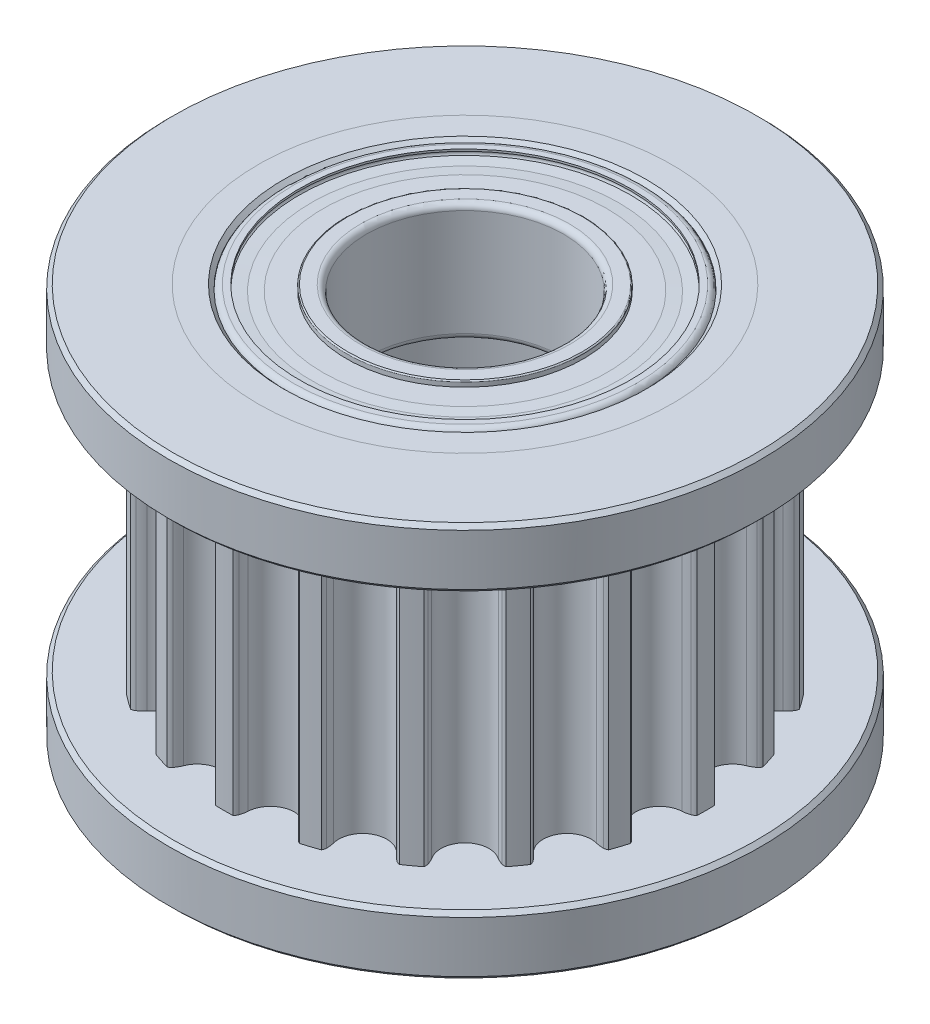
SolidWorks part; units mm, degrees
material "6061-T6 (SS)"
ref_plane "Přední rovina" through (0, 0, 0) normal (0, 0, 1) x (1, 0, 0)
ref_plane "Horní rovina" through (0, 0, 0) normal (0, 1, 0) x (1, 0, 0)
ref_plane "Pravá rovina" through (0, 0, 0) normal (1, 0, 0) x (0, 0, -1)
sketch "Skica1" plane through (0, 0, 0) normal (0, 0, 1) x (1, 0, 0)
  line L0 (4.5, 10) -> (5.25, 10)
  line L1 (5.25, 10) -> (5.25, 8.5)
  line L2 (5.25, 8.5) -> (6.11, 8.5)
  line L3 (6.11, 8.5) -> (6.11, 1.5)
  line L4 (6.11, 1.5) -> (5.25, 1.5)
  line L5 (5.25, 1.5) -> (5.25, 0)
  line L6 (5.25, 0) -> (4.5, 0)
  line L8 (4.5, 10) -> (4.5, 7)
  line L9 (4.5, 7) -> (3.5, 7)
  line L10 (3.5, 7) -> (3.5, 3)
  line L11 (3.5, 3) -> (4.5, 3)
  line L12 (4.5, 3) -> (4.5, 0)
  line L13 (0, 0) -> (0, -4.1646) construction
  dimension "D1" = 10
  dimension "D2" = 7
  dimension "D3" = 4.5
  dimension "D4" = 3.5
  dimension "D5" = 6.11
  dimension "D6" = 3
  dimension "D7" = 5.25
revolve "Rotovat1" add sketch "Skica1" angle 360 about L13
chamfer "Zkosení1" distance 0.1 angle 45 4 edges at (0, 3, 3.5) (0, 0, 4.5) (0, 7, 3.5) (0, 10, 4.5)
fillet "Zaoblit1" radius 0.1 2 edges at (0, 3, 4.5) (0, 7, 4.5)
sketch "Skica11" plane through (0, 8.5, 0) normal (0, 1, 0) x (1, 0, 0)
  line L0 (0, -5.5) -> (0, 5.5) construction
  line L1 (-5.5, 0) -> (5.5, 0) construction
  point P5 (0, 6.1087)
  arc B0 (-3.6824, -4.5256) -> (-4.5256, -3.6824) centre (-4.1938, -4.1938) ccw
  arc B1 (-3.6824, -4.5256) -> (-3.7624, -4.7003) centre (-3.1284, -4.885) ccw
  arc B2 (-3.7624, -4.7003) -> (-3.7672, -4.8088) centre (-3.5429, -4.7643) ccw
  arc B3 (-3.7672, -4.8088) -> (-3.4093, -5.0688) centre (0, 0) ccw
  arc B4 (-3.4093, -5.0688) -> (-3.3076, -5.0308) centre (-3.4362, -4.8418) ccw
  arc B5 (-3.3076, -5.0308) -> (-3.1662, -4.9006) centre (-3.6792, -4.4848) ccw
  arc B6 (-2.1037, -5.442) -> (-3.1662, -4.9006) centre (-2.6926, -5.2845) ccw
  arc B7 (-2.1037, -5.442) -> (-2.1258, -5.6329) centre (-1.4657, -5.6126) ccw
  arc B8 (-2.1258, -5.6329) -> (-2.0968, -5.7376) centre (-1.8973, -5.6259) ccw
  arc B9 (-2.0968, -5.7376) -> (-1.6761, -5.8742) centre (0, 0) ccw
  arc B10 (-1.6761, -5.8742) -> (-1.5911, -5.8066) centre (-1.7719, -5.6667) ccw
  arc B11 (-1.5911, -5.8066) -> (-1.4968, -5.6392) centre (-2.1132, -5.4022) ccw
  arc B12 (-0.319, -5.8257) -> (-1.4968, -5.6392) centre (-0.9278, -5.8579) ccw
  arc B13 (-0.319, -5.8257) -> (-0.2811, -6.0141) centre (0.3404, -5.7909) ccw
  arc B14 (-0.2811, -6.0141) -> (-0.2211, -6.1047) centre (-0.0659, -5.9369) ccw
  arc B15 (-0.2211, -6.1047) -> (0.2211, -6.1047) centre (0, 0) ccw
  arc B16 (0.2211, -6.1047) -> (0.2811, -6.0141) centre (0.0659, -5.9369) ccw
  arc B17 (0.2811, -6.0141) -> (0.319, -5.8257) centre (-0.3404, -5.7909) ccw
  arc B18 (1.4968, -5.6392) -> (0.319, -5.8257) centre (0.9278, -5.8579) ccw
  arc B19 (1.4968, -5.6392) -> (1.5911, -5.8066) centre (2.1132, -5.4022) ccw
  arc B20 (1.5911, -5.8066) -> (1.6761, -5.8742) centre (1.7719, -5.6667) ccw
  arc B21 (1.6761, -5.8742) -> (2.0968, -5.7376) centre (0, 0) ccw
  arc B22 (2.0968, -5.7376) -> (2.1258, -5.6329) centre (1.8973, -5.6259) ccw
  arc B23 (2.1258, -5.6329) -> (2.1037, -5.442) centre (1.4657, -5.6126) ccw
  arc B24 (3.1662, -4.9006) -> (2.1037, -5.442) centre (2.6926, -5.2845) ccw
  arc B25 (3.1662, -4.9006) -> (3.3076, -5.0308) centre (3.6792, -4.4848) ccw
  arc B26 (3.3076, -5.0308) -> (3.4093, -5.0688) centre (3.4362, -4.8418) ccw
  arc B27 (3.4093, -5.0688) -> (3.7672, -4.8088) centre (0, 0) ccw
  arc B28 (3.7672, -4.8088) -> (3.7624, -4.7003) centre (3.5429, -4.7643) ccw
  arc B29 (3.7624, -4.7003) -> (3.6824, -4.5256) centre (3.1284, -4.885) ccw
  arc B30 (4.5256, -3.6824) -> (3.6824, -4.5256) centre (4.1938, -4.1938) ccw
  arc B31 (4.5256, -3.6824) -> (4.7003, -3.7624) centre (4.885, -3.1284) ccw
  arc B32 (4.7003, -3.7624) -> (4.8088, -3.7672) centre (4.7643, -3.5429) ccw
  arc B33 (4.8088, -3.7672) -> (5.0688, -3.4093) centre (0, 0) ccw
  arc B34 (5.0688, -3.4093) -> (5.0308, -3.3076) centre (4.8418, -3.4362) ccw
  arc B35 (5.0308, -3.3076) -> (4.9006, -3.1662) centre (4.4848, -3.6792) ccw
  arc B36 (5.442, -2.1037) -> (4.9006, -3.1662) centre (5.2845, -2.6926) ccw
  arc B37 (5.442, -2.1037) -> (5.6329, -2.1258) centre (5.6126, -1.4657) ccw
  arc B38 (5.6329, -2.1258) -> (5.7376, -2.0968) centre (5.6259, -1.8973) ccw
  arc B39 (5.7376, -2.0968) -> (5.8742, -1.6761) centre (0, 0) ccw
  arc B40 (5.8742, -1.6761) -> (5.8066, -1.5911) centre (5.6667, -1.7719) ccw
  arc B41 (5.8066, -1.5911) -> (5.6392, -1.4968) centre (5.4022, -2.1132) ccw
  arc B42 (5.8257, -0.319) -> (5.6392, -1.4968) centre (5.8579, -0.9278) ccw
  arc B43 (5.8257, -0.319) -> (6.0141, -0.2811) centre (5.7909, 0.3404) ccw
  arc B44 (6.0141, -0.2811) -> (6.1047, -0.2211) centre (5.9369, -0.0659) ccw
  arc B45 (6.1047, -0.2211) -> (6.1047, 0.2211) centre (0, 0) ccw
  arc B46 (6.1047, 0.2211) -> (6.0141, 0.2811) centre (5.9369, 0.0659) ccw
  arc B47 (6.0141, 0.2811) -> (5.8257, 0.319) centre (5.7909, -0.3404) ccw
  arc B48 (5.6392, 1.4968) -> (5.8257, 0.319) centre (5.8579, 0.9278) ccw
  arc B49 (5.6392, 1.4968) -> (5.8066, 1.5911) centre (5.4022, 2.1132) ccw
  arc B50 (5.8066, 1.5911) -> (5.8742, 1.6761) centre (5.6667, 1.7719) ccw
  arc B51 (5.8742, 1.6761) -> (5.7376, 2.0968) centre (0, 0) ccw
  arc B52 (5.7376, 2.0968) -> (5.6329, 2.1258) centre (5.6259, 1.8973) ccw
  arc B53 (5.6329, 2.1258) -> (5.442, 2.1037) centre (5.6126, 1.4657) ccw
  arc B54 (4.9006, 3.1662) -> (5.442, 2.1037) centre (5.2845, 2.6926) ccw
  arc B55 (4.9006, 3.1662) -> (5.0308, 3.3076) centre (4.4848, 3.6792) ccw
  arc B56 (5.0308, 3.3076) -> (5.0688, 3.4093) centre (4.8418, 3.4362) ccw
  arc B57 (5.0688, 3.4093) -> (4.8088, 3.7672) centre (0, 0) ccw
  arc B58 (4.8088, 3.7672) -> (4.7003, 3.7624) centre (4.7643, 3.5429) ccw
  arc B59 (4.7003, 3.7624) -> (4.5256, 3.6824) centre (4.885, 3.1284) ccw
  arc B60 (3.6824, 4.5256) -> (4.5256, 3.6824) centre (4.1938, 4.1938) ccw
  arc B61 (3.6824, 4.5256) -> (3.7624, 4.7003) centre (3.1284, 4.885) ccw
  arc B62 (3.7624, 4.7003) -> (3.7672, 4.8088) centre (3.5429, 4.7643) ccw
  arc B63 (3.7672, 4.8088) -> (3.4093, 5.0688) centre (0, 0) ccw
  arc B64 (3.4093, 5.0688) -> (3.3076, 5.0308) centre (3.4362, 4.8418) ccw
  arc B65 (3.3076, 5.0308) -> (3.1662, 4.9006) centre (3.6792, 4.4848) ccw
  arc B66 (2.1037, 5.442) -> (3.1662, 4.9006) centre (2.6926, 5.2845) ccw
  arc B67 (2.1037, 5.442) -> (2.1258, 5.6329) centre (1.4657, 5.6126) ccw
  arc B68 (2.1258, 5.6329) -> (2.0968, 5.7376) centre (1.8973, 5.6259) ccw
  arc B69 (2.0968, 5.7376) -> (1.6761, 5.8742) centre (0, 0) ccw
  arc B70 (1.6761, 5.8742) -> (1.5911, 5.8066) centre (1.7719, 5.6667) ccw
  arc B71 (1.5911, 5.8066) -> (1.4968, 5.6392) centre (2.1132, 5.4022) ccw
  arc B72 (0.319, 5.8257) -> (1.4968, 5.6392) centre (0.9278, 5.8579) ccw
  arc B73 (0.319, 5.8257) -> (0.2811, 6.0141) centre (-0.3404, 5.7909) ccw
  arc B74 (0.2811, 6.0141) -> (0.2211, 6.1047) centre (0.0659, 5.9369) ccw
  arc B75 (0.2211, 6.1047) -> (-0.2211, 6.1047) centre (0, 0) ccw
  arc B76 (-0.2211, 6.1047) -> (-0.2811, 6.0141) centre (-0.0659, 5.9369) ccw
  arc B77 (-0.2811, 6.0141) -> (-0.319, 5.8257) centre (0.3404, 5.7909) ccw
  arc B78 (-1.4968, 5.6392) -> (-0.319, 5.8257) centre (-0.9278, 5.8579) ccw
  arc B79 (-1.4968, 5.6392) -> (-1.5911, 5.8066) centre (-2.1132, 5.4022) ccw
  arc B80 (-1.5911, 5.8066) -> (-1.6761, 5.8742) centre (-1.7719, 5.6667) ccw
  arc B81 (-1.6761, 5.8742) -> (-2.0968, 5.7376) centre (0, 0) ccw
  arc B82 (-2.0968, 5.7376) -> (-2.1258, 5.6329) centre (-1.8973, 5.6259) ccw
  arc B83 (-2.1258, 5.6329) -> (-2.1037, 5.442) centre (-1.4657, 5.6126) ccw
  arc B84 (-3.1662, 4.9006) -> (-2.1037, 5.442) centre (-2.6926, 5.2845) ccw
  arc B85 (-3.1662, 4.9006) -> (-3.3076, 5.0308) centre (-3.6792, 4.4848) ccw
  arc B86 (-3.3076, 5.0308) -> (-3.4093, 5.0688) centre (-3.4362, 4.8418) ccw
  arc B87 (-3.4093, 5.0688) -> (-3.7672, 4.8088) centre (0, 0) ccw
  arc B88 (-3.7672, 4.8088) -> (-3.7624, 4.7003) centre (-3.5429, 4.7643) ccw
  arc B89 (-3.7624, 4.7003) -> (-3.6824, 4.5256) centre (-3.1284, 4.885) ccw
  arc B90 (-4.5256, 3.6824) -> (-3.6824, 4.5256) centre (-4.1938, 4.1938) ccw
  arc B91 (-4.5256, 3.6824) -> (-4.7003, 3.7624) centre (-4.885, 3.1284) ccw
  arc B92 (-4.7003, 3.7624) -> (-4.8088, 3.7672) centre (-4.7643, 3.5429) ccw
  arc B93 (-4.8088, 3.7672) -> (-5.0688, 3.4093) centre (0, 0) ccw
  arc B94 (-5.0688, 3.4093) -> (-5.0308, 3.3076) centre (-4.8418, 3.4362) ccw
  arc B95 (-5.0308, 3.3076) -> (-4.9006, 3.1662) centre (-4.4848, 3.6792) ccw
  arc B96 (-5.442, 2.1037) -> (-4.9006, 3.1662) centre (-5.2845, 2.6926) ccw
  arc B97 (-5.442, 2.1037) -> (-5.6329, 2.1258) centre (-5.6126, 1.4657) ccw
  arc B98 (-5.6329, 2.1258) -> (-5.7376, 2.0968) centre (-5.6259, 1.8973) ccw
  arc B99 (-5.7376, 2.0968) -> (-5.8742, 1.6761) centre (0, 0) ccw
  arc B100 (-5.8742, 1.6761) -> (-5.8066, 1.5911) centre (-5.6667, 1.7719) ccw
  arc B101 (-5.8066, 1.5911) -> (-5.6392, 1.4968) centre (-5.4022, 2.1132) ccw
  arc B102 (-5.8257, 0.319) -> (-5.6392, 1.4968) centre (-5.8579, 0.9278) ccw
  arc B103 (-5.8257, 0.319) -> (-6.0141, 0.2811) centre (-5.7909, -0.3404) ccw
  arc B104 (-6.0141, 0.2811) -> (-6.1047, 0.2211) centre (-5.9369, 0.0659) ccw
  arc B105 (-6.1047, 0.2211) -> (-6.1047, -0.2211) centre (0, 0) ccw
  arc B106 (-6.1047, -0.2211) -> (-6.0141, -0.2811) centre (-5.9369, -0.0659) ccw
  arc B107 (-6.0141, -0.2811) -> (-5.8257, -0.319) centre (-5.7909, 0.3404) ccw
  arc B108 (-5.6392, -1.4968) -> (-5.8257, -0.319) centre (-5.8579, -0.9278) ccw
  arc B109 (-5.6392, -1.4968) -> (-5.8066, -1.5911) centre (-5.4022, -2.1132) ccw
  arc B110 (-5.8066, -1.5911) -> (-5.8742, -1.6761) centre (-5.6667, -1.7719) ccw
  arc B111 (-5.8742, -1.6761) -> (-5.7376, -2.0968) centre (0, 0) ccw
  arc B112 (-5.7376, -2.0968) -> (-5.6329, -2.1258) centre (-5.6259, -1.8973) ccw
  arc B113 (-5.6329, -2.1258) -> (-5.442, -2.1037) centre (-5.6126, -1.4657) ccw
  arc B114 (-4.9006, -3.1662) -> (-5.442, -2.1037) centre (-5.2845, -2.6926) ccw
  arc B115 (-4.9006, -3.1662) -> (-5.0308, -3.3076) centre (-4.4848, -3.6792) ccw
  arc B116 (-5.0308, -3.3076) -> (-5.0688, -3.4093) centre (-4.8418, -3.4362) ccw
  arc B117 (-5.0688, -3.4093) -> (-4.8088, -3.7672) centre (0, 0) ccw
  arc B118 (-4.8088, -3.7672) -> (-4.7003, -3.7624) centre (-4.7643, -3.5429) ccw
  arc B119 (-4.7003, -3.7624) -> (-4.5256, -3.6824) centre (-4.885, -3.1284) ccw
sketch_block_instance "Blok1-1"
sketch_block "Blok1"
extrude "Odebrat vysunutím1" cut sketch "Skica11" against normal through all flip side to cut
sketch "Skica10" plane through (0, 10, 0) normal (0, 1, 0) x (1, 0, 0)
  circle A0 centre (0, 0) radius 7.5
  circle A1 centre (0, 0) radius 5.25 construction
  circle A2 centre (0, 0) radius 5.25
  dimension "D1" = 15
extrude "Přidat vysunutím1" add sketch "Skica10" against normal up to surface (1.5 mm away) separate body up to face at (0, 8.5, 5.25)
sketch "Skica12" plane through (0, 0, 0) normal (0, -1, 0) x (1, 0, 0)
  circle A0 centre (0, 0) radius 7.5
  circle A1 centre (0, 0) radius 5.25 construction
  circle A2 centre (0, 0) radius 5.25
  circle A3 centre (0, 0) radius 7.5 construction
extrude "Přidat vysunutím2" add sketch "Skica12" against normal up to surface (1.5 mm away) separate body up to face at (0, 1.5, 5.25)
chamfer "Zkosení2" distance 0.1 angle 45 2 edges at (0, 8.5, -7.5) (0, 10, 7.5)
chamfer "Zkosení3" distance 0.1 angle 45 2 edges at (0, 0, -7.5) (0, 1.5, 7.5)
sketch "Skica4" plane through (0, 0, 0) normal (0, 0, 1) x (1, 0, 0)
  line L0 (4.5, 9.85) -> (4.5, 7.15)
  line L1 (4.35, 7) -> (4.2, 7)
  line L2 (4.2, 7) -> (4.2, 7.05)
  line L3 (3.85, 7.2828) -> (4.2132, 7.229)
  line L4 (3.85, 7.2828) -> (3.85, 8.0528)
  line L5 (3.85, 8.9472) -> (3.85, 9.7172)
  line L6 (3.85, 9.7172) -> (4.2132, 9.771)
  line L7 (4.35, 10) -> (4.2, 10)
  line L8 (4.2, 10) -> (4.2, 9.95)
  line L9 (0, 0) -> (0, 18.4294) construction
  line L10 (4.4, 7) -> (-4.4, 7) construction
  arc A0 (4.35, 10) -> (4.5, 9.85) centre (4.35, 9.85) cw
  arc A1 (4.35, 7) -> (4.5, 7.15) centre (4.35, 7.15) ccw
  arc A2 (4.2, 9.95) -> (4.2132, 9.771) centre (4.2, 9.86) cw
  arc A3 (3.85, 8.9472) -> (3.85, 8.0528) centre (3.45, 8.5) cw
  arc A4 (4.2, 7.05) -> (4.2132, 7.229) centre (4.2, 7.14) ccw
  point P26 (4.5, 8.5)
  point P29 (4.275, 7)
  dimension "D3" = 0.09
  dimension "D6" = 0.15
  dimension "D7" = 0.6
  dimension "D1" = 4.5
  dimension "D2" = 3.85
  dimension "D4" = 0.05
  dimension "D5" = 0.15
  dimension "D8" = 0.77
  dimension "D9" = 3
  dimension "D10" = 1.05
revolve "Rotovat2" add sketch "Skica4" angle 360 about L9
sketch "Skica5" plane through (0, 0, 0) normal (0, 0, 1) x (1, 0, 0)
  line L0 (2.5, 9.85) -> (2.5, 7.15)
  line L1 (2.65, 10) -> (2.97, 10)
  line L2 (3, 9.97) -> (3, 9.86)
  line L3 (3, 9.86) -> (3.6, 9.86)
  line L4 (3.6, 9.86) -> (3.9, 9.84)
  line L5 (3.9, 9.84) -> (4.2, 9.86)
  line L6 (4.2, 9.86) -> (4.2, 9.81)
  line L7 (4.2, 9.81) -> (3.9, 9.77)
  line L8 (3.9, 9.77) -> (3.6, 9.77)
  line L9 (3.6, 9.77) -> (3, 9.81)
  line L10 (3, 9.81) -> (3, 8.8969)
  line L11 (2.65, 7) -> (2.97, 7)
  line L12 (0, 0) -> (0, 20.363) construction
  line L13 (3, 7.03) -> (3, 7.14)
  line L21 (3, 7.19) -> (3, 8.1031)
  line L22 (3, 7.14) -> (3.6, 7.14)
  line L23 (3.6, 7.14) -> (3.8962, 7.1917)
  line L24 (3.8962, 7.1917) -> (4.1924, 7.14)
  line L25 (4.1924, 7.14) -> (4.1924, 7.19)
  line L26 (4.1924, 7.19) -> (3.8975, 7.2581)
  line L27 (3.8975, 7.2581) -> (3.5975, 7.2581)
  line L28 (3.5975, 7.2581) -> (3, 7.19)
  line L29 (-4.2, 7) -> (4.2, 7) construction
  arc A0 (2.65, 7) -> (2.5, 7.15) centre (2.65, 7.15) cw
  arc A1 (2.65, 10) -> (2.5, 9.85) centre (2.65, 9.85) ccw
  arc A2 (3, 9.97) -> (2.97, 10) centre (2.97, 9.97) ccw
  arc A3 (3, 7.03) -> (2.97, 7) centre (2.97, 7.03) cw
  arc A4 (3, 8.8969) -> (3, 8.1031) centre (3.45, 8.5) ccw
  dimension "D3" = 0.15
  dimension "D4" = 0.11
  dimension "D5" = 0.03
  dimension "D7" = 0.6
  dimension "D1" = 2.5
  dimension "D2" = 3
  dimension "D6" = 0.6
  dimension "D8" = 0.95
  dimension "D9" = 3
  dimension "D10" = 1.2
  dimension "D11" = 0.3
  dimension "D12" = 0.05
  dimension "D13" = 0.9
  dimension "D14" = 0.6
  dimension "D15" = 0.09
  dimension "D16" = 0.05
  dimension "D17" = 0.05
revolve "Rotovat3" add sketch "Skica5" angle 360 about L12
sketch "Skica6" plane through (0, 0, 0) normal (0, 0, 1) x (1, 0, 0)
  line L0 (3.45, 9.1) -> (3.45, 7.9)
  line L4 (-4.2, 7) -> (4.2, 7) construction
  arc A0 (3.45, 9.1) -> (3.45, 7.9) centre (3.45, 8.5) cw
  dimension "D1" = 0.6
  dimension "D2" = 1.5
  dimension "D3" = 3.45
revolve "Rotovat4" add sketch "Skica6" angle 360 about L0
pattern_circular "Kruhové pole1" count 8 over 360 about axis through (0, 0, 0) along (0, 1, 0) of bodies 105
sketch "Skica7" plane through (0, 0, 0) normal (0, 0, 1) x (1, 0, 0)
  line L0 (4.5, 2.85) -> (4.5, 0.15)
  line L1 (4.35, 0) -> (4.2, 0)
  line L2 (4.2, 0) -> (4.2, 0.05)
  line L3 (3.85, 0.2828) -> (4.2132, 0.229)
  line L4 (3.85, 0.2828) -> (3.85, 1.0528)
  line L5 (3.85, 1.9472) -> (3.85, 2.7172)
  line L6 (3.85, 2.7172) -> (4.2132, 2.771)
  line L7 (4.35, 3) -> (4.2, 3)
  line L8 (4.2, 3) -> (4.2, 2.95)
  line L9 (0, 0) -> (0, 11.2374) construction
  arc A0 (4.35, 3) -> (4.5, 2.85) centre (4.35, 2.85) cw
  arc A1 (4.35, 0) -> (4.5, 0.15) centre (4.35, 0.15) ccw
  arc A2 (4.2, 2.95) -> (4.2132, 2.771) centre (4.2, 2.86) cw
  arc A3 (3.85, 1.9472) -> (3.85, 1.0528) centre (3.45, 1.5) cw
  arc A4 (4.2, 0.05) -> (4.2132, 0.229) centre (4.2, 0.14) ccw
  point P19 (4.5, 1.5)
  point P20 (4.275, 0)
  dimension "D1" = 0.09
  dimension "D4" = 0.15
  dimension "D5" = 0.6
  dimension "D2" = 0.05
  dimension "D3" = 0.15
  dimension "D6" = 0.77
  dimension "D7" = 3
  dimension "D8" = 1.05
  dimension "D9" = 4.5
  dimension "D10" = 3.85
revolve "Rotovat5" add sketch "Skica7" angle 360 about L9
sketch "Skica8" plane through (0, 0, 0) normal (0, 0, 1) x (1, 0, 0)
  line L0 (2.5, 2.85) -> (2.5, 0.15)
  line L1 (2.65, 3) -> (2.97, 3)
  line L2 (3, 2.97) -> (3, 2.86)
  line L3 (3, 2.86) -> (3.6, 2.86)
  line L4 (3.6, 2.86) -> (3.9, 2.84)
  line L5 (3.9, 2.84) -> (4.2, 2.86)
  line L6 (4.2, 2.86) -> (4.2, 2.81)
  line L7 (4.2, 2.81) -> (3.9, 2.77)
  line L8 (3.9, 2.77) -> (3.6, 2.77)
  line L9 (3.6, 2.77) -> (3, 2.81)
  line L10 (3, 2.81) -> (3, 1.8969)
  line L11 (2.65, 0) -> (2.97, 0)
  line L12 (3, 0.03) -> (3, 0.14)
  line L13 (3, 0.19) -> (3, 1.1031)
  line L14 (3, 0.14) -> (3.6, 0.14)
  line L15 (3.6, 0.14) -> (3.8962, 0.1917)
  line L16 (3.8962, 0.1917) -> (4.1924, 0.14)
  line L17 (4.1924, 0.14) -> (4.1924, 0.19)
  line L18 (4.1924, 0.19) -> (3.8975, 0.2581)
  line L19 (3.8975, 0.2581) -> (3.5975, 0.2581)
  line L20 (3.5975, 0.2581) -> (3, 0.19)
  line L21 (0, 0) -> (0, -2.9362) construction
  arc A0 (2.65, 0) -> (2.5, 0.15) centre (2.65, 0.15) cw
  arc A1 (2.65, 3) -> (2.5, 2.85) centre (2.65, 2.85) ccw
  arc A2 (3, 2.97) -> (2.97, 3) centre (2.97, 2.97) ccw
  arc A3 (3, 0.03) -> (2.97, 0) centre (2.97, 0.03) cw
  arc A4 (3, 1.8969) -> (3, 1.1031) centre (3.45, 1.5) ccw
  dimension "D1" = 0.15
  dimension "D2" = 0.03
  dimension "D5" = 0.6
  dimension "D3" = 0.11
  dimension "D4" = 0.6
  dimension "D6" = 0.95
  dimension "D7" = 3
  dimension "D8" = 1.2
  dimension "D9" = 0.3
  dimension "D10" = 0.05
  dimension "D11" = 0.9
  dimension "D12" = 0.6
  dimension "D13" = 0.09
  dimension "D14" = 0.05
  dimension "D15" = 0.05
  dimension "D16" = 2.5
  dimension "D17" = 3
revolve "Rotovat6" add sketch "Skica8" angle 360 about L21
sketch "Skica9" plane through (0, 0, 0) normal (0, 0, 1) x (1, 0, 0)
  line L0 (3.45, 2.1) -> (3.45, 0.9)
  line L1 (0, -2.351) -> (0, 5.6956) construction
  arc A0 (3.45, 2.1) -> (3.45, 0.9) centre (3.45, 1.5) cw
  dimension "D1" = 0.6
  dimension "D2" = 3.45
  dimension "D3" = 1.5
revolve "Rotovat7" add sketch "Skica9" angle 360 about L0
pattern_circular "Kruhové pole3" count 8 over 360 about axis through (0, 0, 0) along (0, 1, 0) of bodies 123
